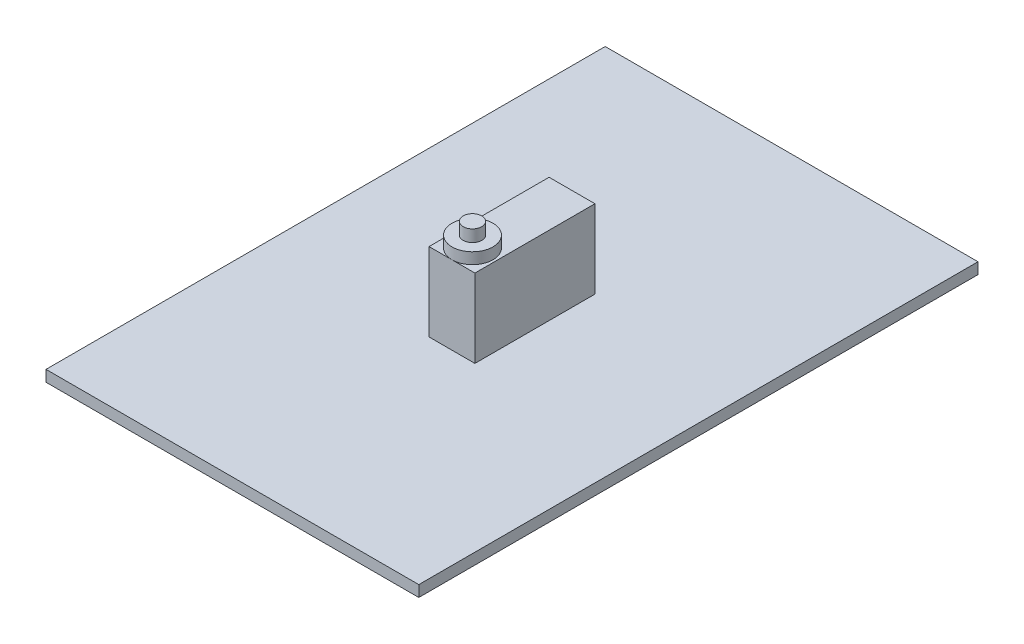
SolidWorks part; units mm, degrees
ref_plane "Front Plane" through (0, 0, 0) normal (0, 0, 1) x (1, 0, 0)
ref_plane "Top Plane" through (0, 0, 0) normal (0, 1, 0) x (1, 0, 0)
ref_plane "Right Plane" through (0, 0, 0) normal (1, 0, 0) x (0, 0, -1)
sketch "Sketch2" plane through (0, 0, 0) normal (0, 0, 1) x (1, 0, 0)
  line L1 (50, -1.5) -> (-50, -1.5)
  line L2 (50, -1.5) -> (50, 1.5)
  line L3 (50, 1.5) -> (-50, 1.5)
  line L4 (-50, -1.5) -> (-50, 1.5)
  line L5 (50, -1.5) -> (-50, 1.5) construction
  line L6 (50, 1.5) -> (-50, -1.5) construction
  point P0 (0, 0)
  dimension "D1" = 3
  dimension "D2" = 100
extrude "Boss-Extrude2" add sketch "Sketch2" against normal blind 150
sketch "Sketch3" plane through (0, 0, 0) normal (0, 1, 0) x (1, 0, 0)
  line L0 (-50, 150) -> (50, 0) construction
  line L1 (50, 150) -> (-50, 0) construction
  line L3 (6.15, 58.9) -> (-6.15, 58.9)
  line L4 (6.15, 58.9) -> (6.15, 91.1)
  line L5 (6.15, 91.1) -> (-6.15, 91.1)
  line L6 (-6.15, 58.9) -> (-6.15, 91.1)
  line L7 (6.15, 58.9) -> (-6.15, 91.1) construction
  line L8 (6.15, 91.1) -> (-6.15, 58.9) construction
  point P8 (0, 75)
  dimension "D1" = 12.3
  dimension "D2" = 32.2
extrude "Boss-Extrude3" add sketch "Sketch3" along normal blind 22.5
sketch "Sketch4" plane through (0, 22.5, 0) normal (0, 1, 0) x (1, 0, 0)
  line L0 (6.15, 58.9) -> (6.15, 64.4)
  line L1 (6.15, 91.1) -> (6.15, 58.9) construction
  line L2 (6.15, 64.4) -> (0, 64.4)
  circle A0 centre (0, 64.4) radius 5.5
  dimension "D1" = 5.5
extrude "Boss-Extrude4" add sketch "Sketch4" along normal blind 3 contours A0
sketch "Sketch10" plane through (0, 25.5, 0) normal (0, 1, 0) x (1, 0, 0)
  circle A0 centre (0, 64.4) radius 2.5
  dimension "D1" = 5
extrude "Boss-Extrude5" add sketch "Sketch10" along normal blind 3.2
